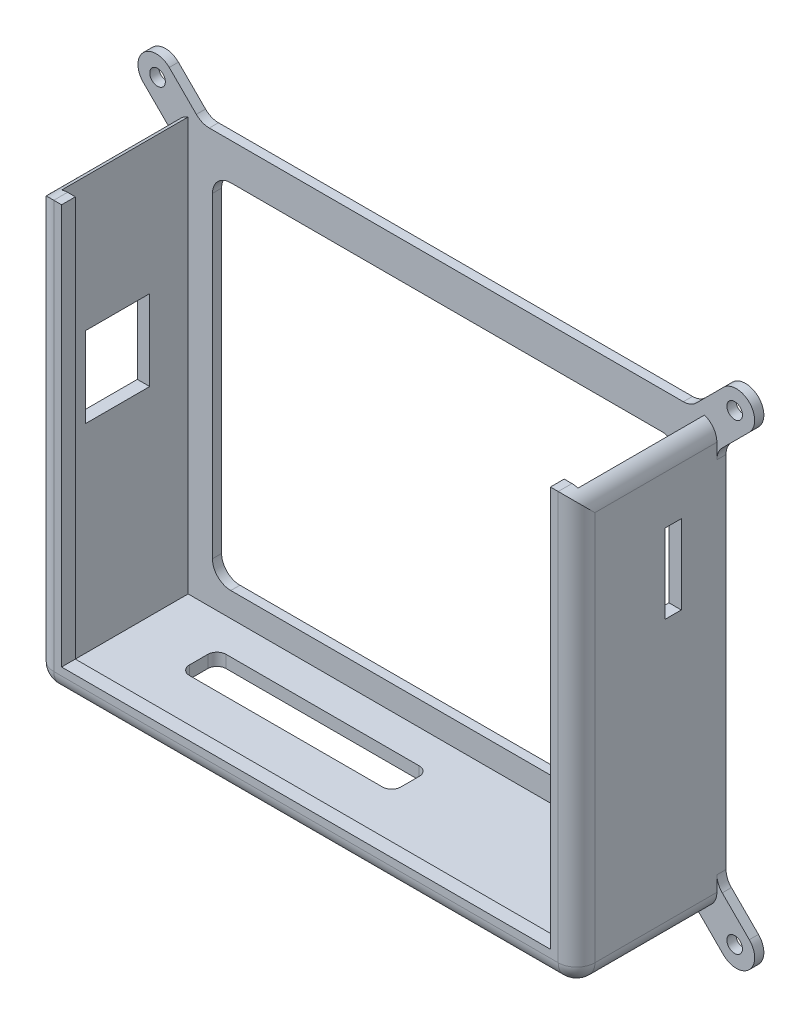
SolidWorks part; units mm, degrees
ref_plane "Front Plane" through (0, 0, 0) normal (0, 0, 1) x (1, 0, 0)
ref_plane "Top Plane" through (0, 0, 0) normal (0, 1, 0) x (1, 0, 0)
ref_plane "Right Plane" through (0, 0, 0) normal (1, 0, 0) x (0, 0, -1)
sketch "Sketch1" plane through (0, 0, 0) normal (0, 0, 1) x (1, 0, 0)
  line L0 (8, 85) -> (-2, 95) construction
  line L1 (5.6569, 0) -> (112.3431, 0)
  line L2 (0, 5.6569) -> (0, 87.3431)
  line L3 (5.6569, 93) -> (112.3431, 93)
  line L4 (118, 5.6569) -> (118, 87.3431)
  line L5 (8, 85) -> (110, 85)
  line L6 (8, 85) -> (8, 8)
  line L7 (8, 8) -> (110, 8)
  line L8 (110, 85) -> (110, 8)
  line L9 (120, 95) -> (110, 85) construction
  line L10 (-1.3294, -1.3294) -> (8, 8) construction
  line L11 (120, -2) -> (110, 8) construction
  line L12 (0, 87.3431) -> (-7.0711, 94.4142)
  line L13 (5.6569, 93) -> (-1.4142, 100.0711)
  line L14 (5.6569, 93) -> (0, 93) construction
  line L15 (0, 93) -> (0, 87.3431) construction
  line L16 (112.3431, 93) -> (119.4142, 100.0711)
  line L17 (118, 87.3431) -> (125.0711, 94.4142)
  line L18 (112.3431, 93) -> (118, 93) construction
  line L19 (118, 93) -> (118, 87.3431) construction
  line L20 (112.3431, 0) -> (119.4142, -7.0711)
  line L21 (118, 5.6569) -> (125.0711, -1.4142)
  line L22 (112.3431, 0) -> (118, 0) construction
  line L23 (118, 0) -> (118, 5.6569) construction
  line L24 (0, 5.6569) -> (-7.0711, -1.4142)
  line L25 (5.6569, 0) -> (-1.4142, -7.0711)
  line L26 (5.6569, 0) -> (0, 0) construction
  line L27 (0, 0) -> (0, 5.6569) construction
  arc A0 (-1.4142, 100.0711) -> (-7.0711, 94.4142) centre (-4.2426, 97.2426) ccw
  arc A1 (125.0711, 94.4142) -> (119.4142, 100.0711) centre (122.2426, 97.2426) ccw
  arc A2 (119.4142, -7.0711) -> (125.0711, -1.4142) centre (122.2426, -4.2426) ccw
  arc A3 (-7.0711, -1.4142) -> (-1.4142, -7.0711) centre (-4.2426, -4.2426) ccw
  dimension "D7" = 8
  dimension "D8" = 10
  dimension "D1" = 118
  dimension "D2" = 93
  dimension "D3" = 8
  dimension "D4" = 8
  dimension "D5" = 8
  dimension "D6" = 8
  dimension "D9" = 10
  dimension "D10" = 10
  dimension "D11" = 10
extrude "Boss-Extrude1" add sketch "Sketch1" along normal blind 2
sketch "Sketch2" plane through (0, 0, 2) normal (0, 0, 1) x (1, 0, 0)
  line L0 (0, 93) -> (0, 0)
  line L1 (0, 0) -> (118, 0)
  line L2 (118, 0) -> (118, 93)
  line L3 (118, 93) -> (115.3, 93)
  line L4 (115.3, 93) -> (115.3, 2.7)
  line L5 (115.3, 2.7) -> (2.7, 2.7)
  line L6 (2.7, 2.7) -> (2.7, 93)
  line L7 (2.7, 93) -> (0, 93)
  line L9 (112.3431, 93) -> (5.6569, 93) construction
  point P3 (0, 0)
  point P14 (0, 0)
  dimension "D1" = 2.7
  dimension "D2" = 2.7
  dimension "D3" = 2.7
extrude "Boss-Extrude2" add sketch "Sketch2" along normal blind 27.6
fillet "Fillet1" radius 4 4 edges at (8, 8, 1) (110, 8, 1) (110, 85, 1) (8, 85, 1)
fillet "Fillet3" radius 4 8 edges at (112.3431, 93, 1) (5.6569, 93, 1) (0, 87.3431, 1) (0, 5.6569, 1) (5.6569, 0, 1) (112.3431, 0, 1) (118, 5.6569, 1) (118, 87.3431, 1)
hole_wizard "M3 Clearance Hole1" positions "Sketch3" profile "Sketch4" hole size "M3" standard "ANSI Metric" end condition through all
sketch "Sketch3" plane through (0, 0, 2) normal (0, 0, 1) x (1, 0, 0)
  point P0 (-3.9725, 96.9238)
  point P2 (121.8743, 96.9238)
  point P4 (121.8743, -3.9136)
  point P6 (-3.9725, -3.9136)
sketch "Sketch4" plane through (-3.9725, 96.9238, 2) normal (1, 0, 0) x (0, -1, 0)
  line L0 (0, 0) -> (0, 2)
  line L1 (0, 2) -> (1.7, 2)
  line L2 (1.7, 2) -> (1.7, 0)
  line L5 (1.7, 0) -> (0, 0)
  line L11 (0, -6.35) -> (0, 107.95) construction
  dimension "Thru Hole Dia." = 3.4
  dimension "Thru Hole Depth" = 2
sketch "Sketch5" plane through (0, 0, 29.6) normal (0, 0, 1) x (1, 0, 0)
  line L0 (0, 93) -> (5.7, 93)
  line L1 (5.7, 93) -> (5.7, 5.7)
  line L2 (5.7, 5.7) -> (112.3, 5.7)
  line L3 (112.3, 5.7) -> (112.3, 93)
  line L4 (112.3, 93) -> (118, 93)
  line L5 (118, 93) -> (118, 0)
  line L6 (118, 0) -> (0, 0)
  line L7 (0, 0) -> (0, 93)
  line L8 (2.7, 2.7) -> (2.7, 93) construction
  line L9 (115.3, 2.7) -> (2.7, 2.7) construction
  line L10 (115.3, 93) -> (115.3, 2.7) construction
  dimension "D1" = 3
  dimension "D2" = 3
  dimension "D3" = 3
extrude "Boss-Extrude3" add sketch "Sketch5" along normal blind 3
fillet "Fillet4" radius 4 7 edges at (0, 0, 17.3) (118, 0, 17.3) (118, 93, 17.3) (0, 93, 17.3) (59, 0, 32.6) (118, 46.5, 32.6) (0, 46.5, 32.6)
sketch "Sketch6" plane through (0, 0, 0) normal (-1, 0, 0) x (0, 0, 1)
  line L0 (24.377, 46.0619) -> (24.377, 62.8513) construction
  line L1 (10.377, 63.6119) -> (24.377, 63.6119)
  line L2 (10.377, 63.6119) -> (10.377, 46.0619)
  line L3 (10.377, 46.0619) -> (24.377, 46.0619)
  line L4 (24.377, 63.6119) -> (24.377, 46.0619)
  line L5 (24.377, 46.0619) -> (10.7626, 46.0619) construction
  point P6 (24.377, 54.4566)
  point P7 (24.377, 54.8369)
  point P10 (17.5698, 46.0619)
  point P11 (17.377, 46.0619)
  dimension "D1" = 17.55
  dimension "D2" = 14
extrude "Cut-Extrude1" cut sketch "Sketch6" against normal blind 5
sketch "Sketch8" plane through (0, 0, 0) normal (0, -1, 0) x (1, 0, 0)
  line L0 (17.745, 15.7626) -> (17.745, 10.7626) construction
  line L1 (16.245, 9.2626) -> (62.345, 9.2626)
  line L2 (16.245, 9.2626) -> (16.245, 17.2626)
  line L3 (16.245, 17.2626) -> (62.345, 17.2626)
  line L4 (62.345, 9.2626) -> (62.345, 17.2626)
  line L5 (60.845, 15.7626) -> (60.845, 10.7626) construction
  line L6 (48.225, 15.7626) -> (53.225, 15.7626) construction
  line L7 (60.845, 10.7626) -> (55.845, 10.7626) construction
  dimension "D1" = 1.5
  dimension "D2" = 1.5
  dimension "D3" = 1.5
  dimension "D4" = 1.5
extrude "Cut-Extrude3" cut sketch "Sketch8" against normal blind 5
sketch "Sketch9" plane through (118, 0, 0) normal (1, 0, 0) x (0, 0, -1)
  line L0 (-11.0166, 62.2083) -> (-13.0486, 62.2083) construction
  line L1 (-13.3526, 61.2083) -> (-9.7626, 61.2083)
  line L2 (-13.3526, 61.2083) -> (-13.3526, 78.4483)
  line L3 (-13.3526, 78.4483) -> (-9.7626, 78.4483)
  line L4 (-9.7626, 61.2083) -> (-9.7626, 78.4483)
  line L5 (-13.0486, 77.4483) -> (-11.0166, 77.4483) construction
  line L6 (-12.3526, 76.4983) -> (-12.3526, 75.8583) construction
  line L7 (-10.7626, 77.1943) -> (-10.7626, 75.1623) construction
  dimension "D1" = 1
  dimension "D2" = 1
  dimension "D3" = 1
  dimension "D4" = 1
extrude "Cut-Extrude4" cut sketch "Sketch9" against normal blind 5
fillet "Fillet5" radius 2 4 edges at (16.245, 1.35, 9.2626) (16.245, 1.35, 17.2626) (62.345, 1.35, 17.2626) (62.345, 1.35, 9.2626)
